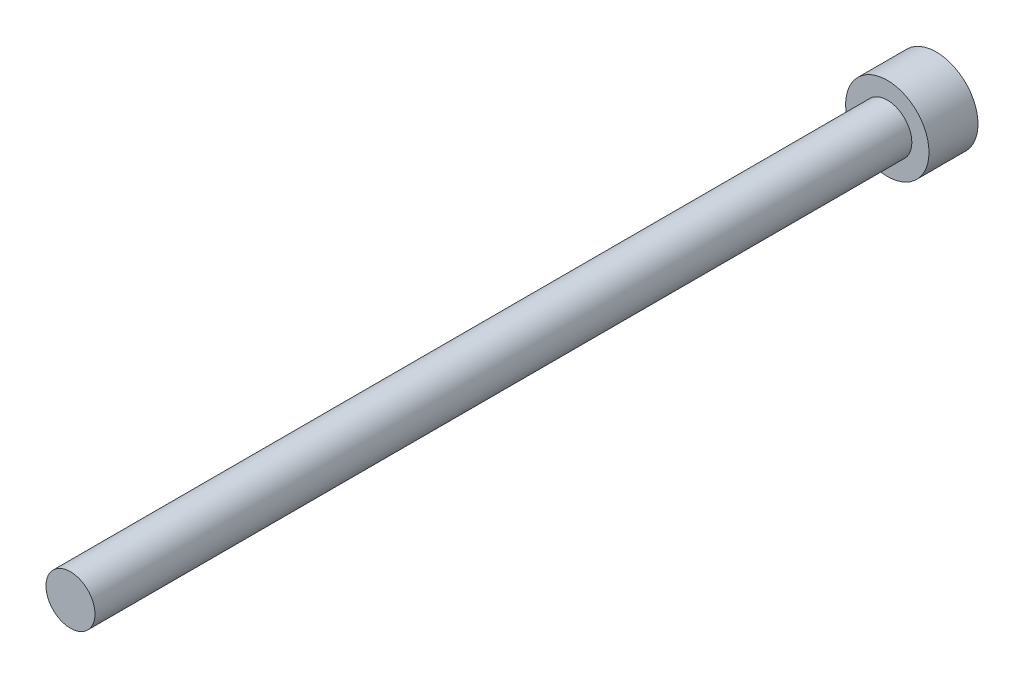
SolidWorks part; units mm, degrees
ref_plane "前视基准面" through (0, 0, 0) normal (0, 0, 1) x (1, 0, 0)
ref_plane "上视基准面" through (0, 0, 0) normal (0, 1, 0) x (1, 0, 0)
ref_plane "右视基准面" through (0, 0, 0) normal (1, 0, 0) x (0, 0, -1)
sketch "草图1" plane through (0, 0, 0) normal (0, 0, 1) x (1, 0, 0)
  circle A0 centre (0, 0) radius 5.1
  dimension "D1" = 10.2
extrude "凸台-拉伸1" add sketch "草图1" along normal blind 6
sketch "草图2" plane through (0, 0, 6) normal (0, 0, 1) x (1, 0, 0)
  circle A0 centre (0, 0) radius 3
  dimension "D1" = 6
extrude "凸台-拉伸2" add sketch "草图2" along normal blind 100
